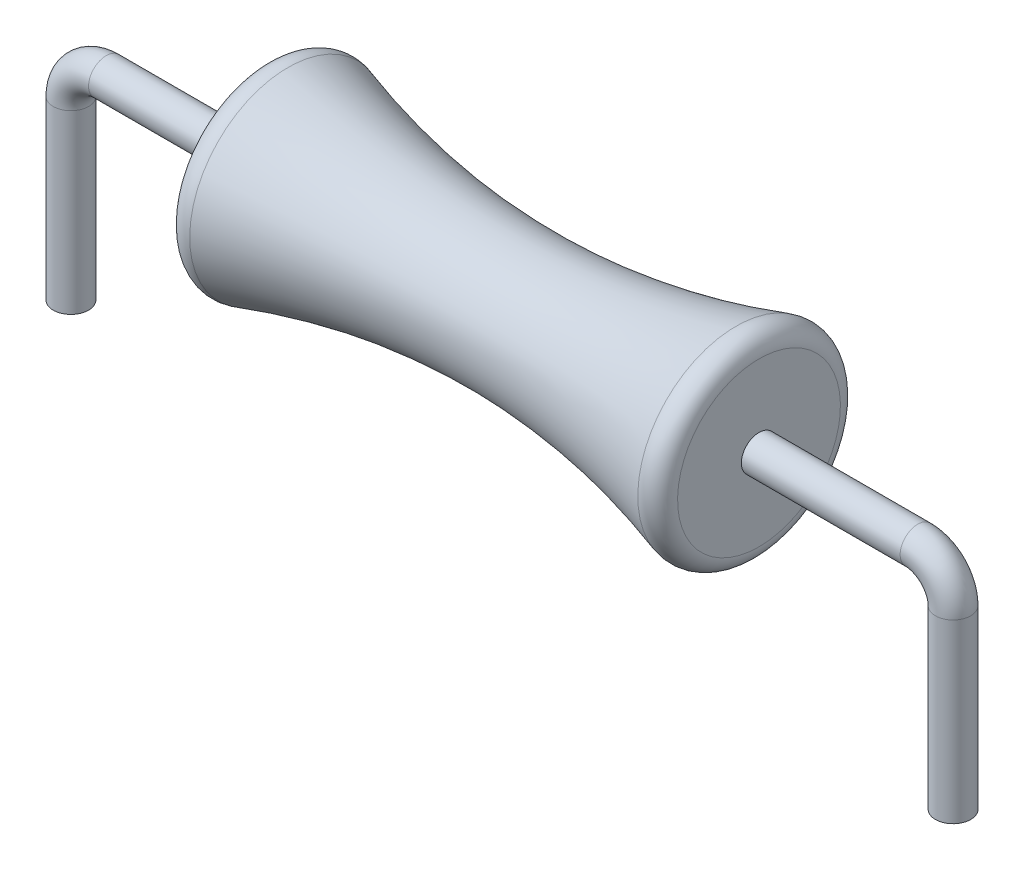
SolidWorks part; units mm, degrees
ref_plane "Front" through (0, 0, 0) normal (0, 0, 1) x (1, 0, 0)
ref_plane "Top" through (0, 0, 0) normal (0, 1, 0) x (1, 0, 0)
ref_plane "Right" through (0, 0, 0) normal (1, 0, 0) x (0, 0, -1)
sketch "Sketch1" plane through (0, 0, 0) normal (0, 0, 1) x (1, 0, 0)
  line L0 (-3.5, 0) -> (3.5, 0)
  line L1 (3.5, 0) -> (3.5, 1.5)
  line L2 (-3.5, 0) -> (-3.5, 1.5)
  spline S0 degree 2 poles (-3.5, 1.5) (0, 0.2825) (3.5, 1.5) knots 0 0 0 1 1 1
  point P7 (0, 0)
  dimension "D1" = 7
  dimension "D2" = 1.5
  dimension "D3" = 1.5
revolve "Revolve1" add sketch "Sketch1" angle 360 about L0
fillet "Fillet2" radius 0.25 2 edges at (-3.5, -1.5, 0) (3.5, -1.5, 0)
sketch "Sketch3" plane through (0, 0, 0) normal (0, 0, 1) x (1, 0, 0)
  line L0 (3.5, 0) -> (5.75, 0)
  line L2 (6.25, -0.5) -> (6.25, -3)
  line L3 (3.5, 1.1537) -> (3.5, -1.1537) construction
  arc A0 (5.75, 0) -> (6.25, -0.5) centre (5.75, -0.5) cw
  point P7 (3.5, 0)
  dimension "D2" = 0.5
  dimension "D1" = 2.25
  dimension "D3" = 2.5
sketch "Sketch4" plane through (3.5, 0, 0) normal (1, 0, 0) x (0, 0, -1)
  circle A0 centre (0, 0) radius 0.25
  dimension "D1" = 0.5
sweep "Sweep1" add profiles "Sketch4" path "Sketch3"
mirror "Mirror1" about plane through (0, 0, 0) normal (1, 0, 0) of "Sweep1"
